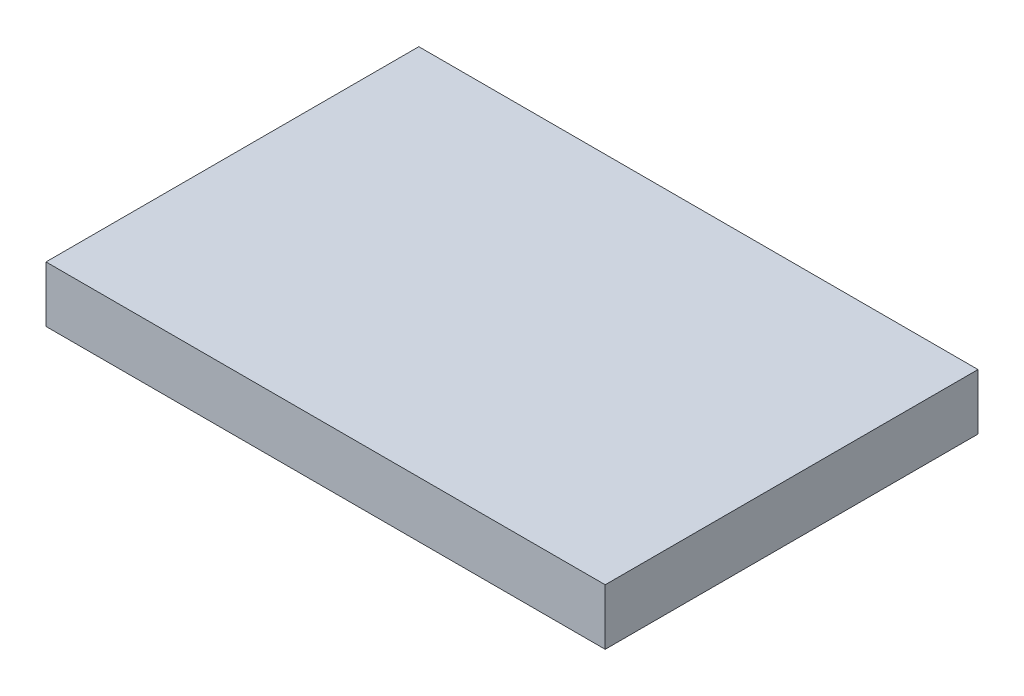
SolidWorks part; units mm, degrees
material "6061-T6 (SS)"
ref_plane "Front Plane" through (0, 0, 0) normal (0, 0, 1) x (1, 0, 0)
ref_plane "Top Plane" through (0, 0, 0) normal (0, 1, 0) x (1, 0, 0)
ref_plane "Right Plane" through (0, 0, 0) normal (1, 0, 0) x (0, 0, -1)
sketch "Sketch1" plane through (0, 0, 0) normal (0, 1, 0) x (1, 0, 0)
  line L1 (-15, -10) -> (15, -10)
  line L2 (-15, -10) -> (-15, 10)
  line L3 (-15, 10) -> (15, 10)
  line L4 (15, -10) -> (15, 10)
  line L5 (-15, -10) -> (15, 10) construction
  line L6 (-15, 10) -> (15, -10) construction
  point P0 (0, 0)
  dimension "D1" = 20
  dimension "D2" = 30
extrude "Boss-Extrude1" add sketch "Sketch1" along normal blind 3
